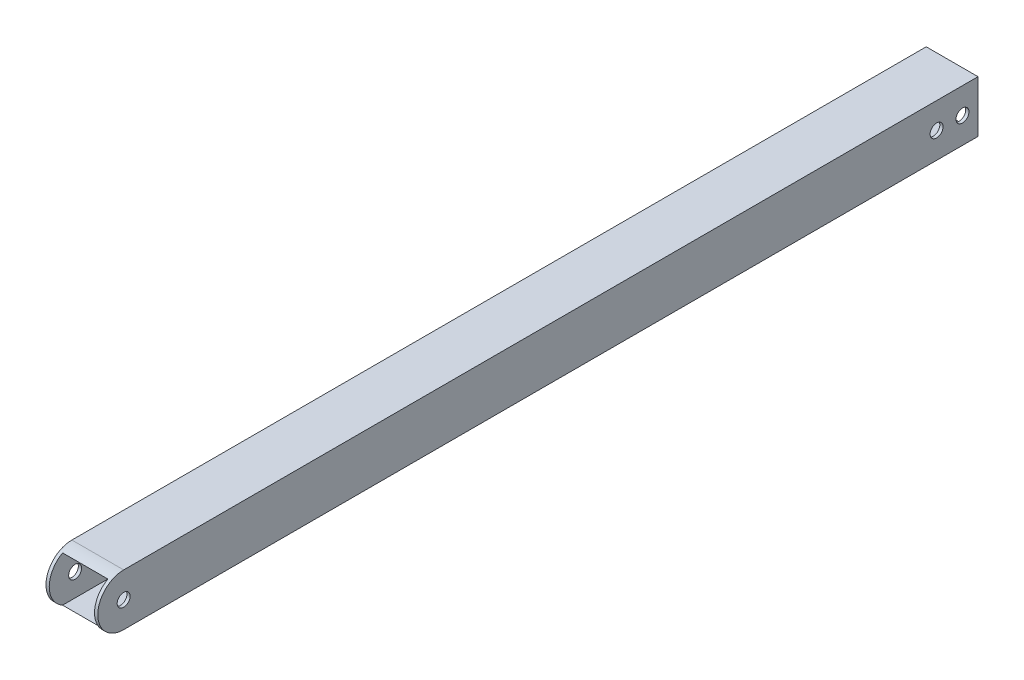
SolidWorks part; units mm, degrees
ref_plane "Front Plane" through (0, 0, 0) normal (0, 0, 1) x (1, 0, 0)
ref_plane "Top Plane" through (0, 0, 0) normal (0, 1, 0) x (1, 0, 0)
ref_plane "Right Plane" through (0, 0, 0) normal (1, 0, 0) x (0, 0, -1)
sketch "Sketch1" plane through (0, 0, 0) normal (0, 0, 1) x (1, 0, 0)
  line L0 (-11.1125, 11.1125) -> (11.1125, 11.1125)
  line L1 (-12.7, 12.7) -> (12.7, 12.7)
  line L2 (-12.7, 12.7) -> (-12.7, -12.7)
  line L3 (-12.7, -12.7) -> (12.7, -12.7)
  line L4 (12.7, 12.7) -> (12.7, -12.7)
  line L5 (-12.7, 12.7) -> (12.7, -12.7) construction
  line L6 (-12.7, -12.7) -> (12.7, 12.7) construction
  line L7 (11.1125, 11.1125) -> (11.1125, -11.1125)
  line L8 (-11.1125, -11.1125) -> (11.1125, -11.1125)
  line L9 (-11.1125, 11.1125) -> (-11.1125, -11.1125)
  point P0 (0, 0)
  dimension "D1" = 25.4
  dimension "1" = 25.4
  dimension "D2" = 1.5875
extrude "Boss-Extrude1" add sketch "Sketch1" along normal blind 431.8
sketch "Sketch2" plane through (12.7, 0, 0) normal (1, 0, 0) x (0, 0, -1)
  line L0 (-431.8, -12.7) -> (-431.8, 12.7) construction
  line L1 (-431.8, -12.7) -> (0, -12.7) construction
  circle A0 centre (-419.1, 0) radius 3.175
  circle A1 centre (-7.62, 0) radius 3.175
  circle A2 centre (-20.32, 0) radius 3.175
  dimension "D1" = 6.35
  dimension "D4" = 6.35
  dimension "D5" = 6.35
  dimension "D2" = 12.7
  dimension "D3" = 12.7
  dimension "D6" = 7.62
  dimension "D7" = 12.7
  dimension "D8" = 12.7
  dimension "D9" = 12.7
extrude "Cut-Extrude1" cut sketch "Sketch2" against normal through all
sketch "Sketch4" plane through (12.7, 0, 0) normal (1, 0, 0) x (0, 0, -1)
  line L0 (-431.8, 12.7) -> (-419.1, 12.7) construction
  line L1 (-431.8, 12.7) -> (0, 12.7) construction
  line L2 (-419.1, 12.7) -> (-419.1, -12.7) construction
  line L3 (-431.8, -12.7) -> (0, -12.7) construction
  line L4 (-419.1, 12.7) -> (-431.8, 12.7)
  line L5 (-431.8, 12.7) -> (-491.49, -12.7)
  line L6 (-491.49, -12.7) -> (-419.1, -12.7)
  arc A0 (-419.1, 12.7) -> (-419.1, -12.7) centre (-419.1, 0) ccw
  point P9 (0, 0)
  line M4 (0, 12.7) -> (-431.8, 12.7)
  line M5 (-431.8, 12.7) -> (-431.8, -12.7)
  line M6 (-431.8, -12.7) -> (0, -12.7)
  dimension "D1" = 12.7
extrude "Cut-Extrude2" cut sketch "Sketch4" against normal blind 491.49 contours A0 M4 M5 | A0 L5 M6
